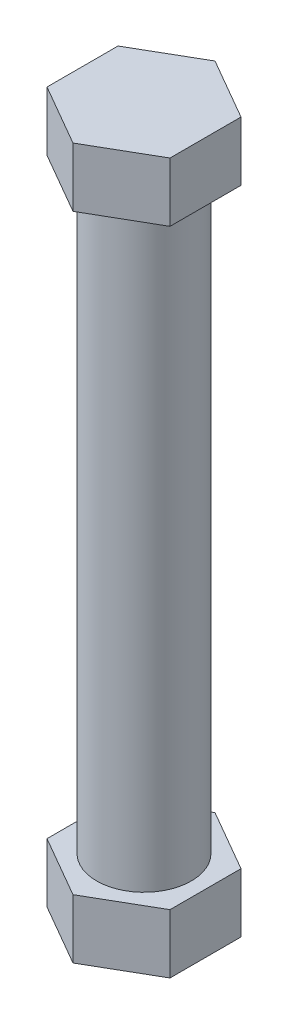
SolidWorks part; units mm, degrees
ref_plane "Front Plane" through (0, 0, 0) normal (0, 0, 1) x (1, 0, 0)
ref_plane "Top Plane" through (0, 0, 0) normal (0, 1, 0) x (1, 0, 0)
ref_plane "Right Plane" through (0, 0, 0) normal (1, 0, 0) x (0, 0, -1)
sketch "Sketch1" plane through (0, 0, 0) normal (0, 1, 0) x (1, 0, 0)
  circle A0 centre (0, 0) radius 10.16
  dimension "D1" = 20.32
extrude "Boss-Extrude1" add sketch "Sketch1" along normal blind 127
sketch "Sketch2" plane through (0, 127, 0) normal (0, 1, 0) x (1, 0, 0)
  line L1 (0, 15.24) -> (-13.1982, 7.62)
  line L2 (-13.1982, 7.62) -> (-13.1982, -7.62)
  line L3 (-13.1982, -7.62) -> (0, -15.24)
  line L4 (0, -15.24) -> (13.1982, -7.62)
  line L5 (13.1982, -7.62) -> (13.1982, 7.62)
  line L6 (13.1982, 7.62) -> (0, 15.24)
  circle A0 centre (0, 0) radius 13.1982 construction
  point P1 (0, 0)
  point P10 (0, 0)
  point P11 (0, 0)
  dimension "D1" = 15.24
extrude "Boss-Extrude2" add sketch "Sketch2" along normal blind 12.7
sketch "Sketch3" plane through (0, 0, 0) normal (0, -1, 0) x (1, 0, 0)
  line L1 (-13.1982, 7.62) -> (-13.1982, -7.62)
  line L2 (-13.1982, -7.62) -> (0, -15.24)
  line L3 (0, -15.24) -> (13.1982, -7.62)
  line L4 (13.1982, -7.62) -> (13.1982, 7.62)
  line L5 (13.1982, 7.62) -> (0, 15.24)
  line L6 (0, 15.24) -> (-13.1982, 7.62)
  circle A0 centre (0, 0) radius 13.1982 construction
  point P1 (0, 0)
  dimension "D1" = 15.24
extrude "Boss-Extrude3" add sketch "Sketch3" along normal blind 12.7
